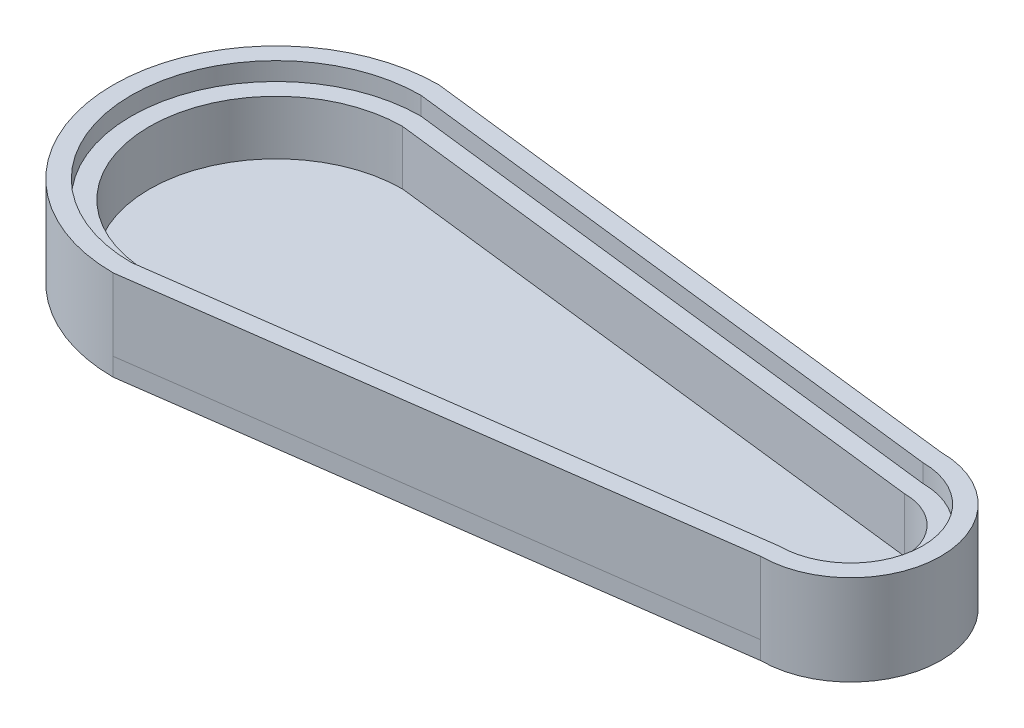
SolidWorks part; units mm, degrees
ref_plane "Front Plane" through (0, 0, 0) normal (0, 0, 1) x (1, 0, 0)
ref_plane "Top Plane" through (0, 0, 0) normal (0, 1, 0) x (1, 0, 0)
ref_plane "Right Plane" through (0, 0, 0) normal (1, 0, 0) x (0, 0, -1)
sketch "Sketch1" plane through (0, 0, 0) normal (0, 1, 0) x (1, 0, 0)
  line L0 (0, 50.8924) -> (200.0001, 27.3028)
  line L1 (199.9996, -23.3818) -> (0, -50.8924)
  line L2 (0.0003, 57.2427) -> (199.9998, 33.6531)
  line L3 (-0.0015, -57.2427) -> (199.9993, -29.7322)
  arc A0 (0, -50.8924) -> (0, 50.8924) centre (0, 0) cw
  arc A1 (199.9996, -23.3818) -> (200.0001, 27.3028) centre (199.9996, 1.9605) ccw
  arc A2 (-0.0015, -57.2427) -> (0.0003, 57.2427) centre (0, 0) cw
  arc A3 (199.9993, -29.7322) -> (199.9998, 33.6531) centre (199.9996, 1.9605) ccw
  dimension "D1" = 6.3066
extrude "Boss-Extrude1" add sketch "Sketch1" along normal blind 6.35 contours L3 A3 L2 A2
sketch "Sketch5" plane through (0, 6.35, 0) normal (0, 1, 0) x (1, 0, 0)
  line L0 (0.0003, 57.2427) -> (199.9998, 33.6531)
  line L1 (-0.0015, -57.2427) -> (199.9996, -29.7322)
  line L4 (-0.1062, 44.55) -> (199.8933, 20.9505)
  line L5 (-0.1062, -44.55) -> (199.8933, -17.0295)
  arc A0 (0.0003, 57.2427) -> (-0.0015, -57.2427) centre (0, 0) ccw
  arc A1 (0.0003, 57.2427) -> (-0.0015, -57.2427) centre (0, 0) ccw construction
  arc A2 (199.9996, -29.7322) -> (199.9998, 33.6531) centre (199.9996, 1.9605) ccw
  arc A3 (199.9993, -29.7322) -> (199.9998, 33.6531) centre (199.9996, 1.9605) ccw construction
  arc A6 (-0.1062, 44.55) -> (-0.1062, -44.55) centre (0, 0) ccw
  arc A7 (199.8933, 20.9505) -> (199.8933, -17.0295) centre (199.9996, 1.9605) cw
extrude "Boss-Extrude3" add sketch "Sketch5" along normal blind 25.4
sketch "Sketch6" plane through (0, 31.75, 0) normal (0, 1, 0) x (1, 0, 0)
  line L0 (0, 50.9) -> (199.9996, 27.3005)
  line L1 (0, -50.9) -> (199.9996, -23.3795)
  arc A0 (0, 50.9) -> (0, -50.9) centre (0, 0) ccw
  arc A1 (199.9996, -23.3795) -> (199.9996, 27.3005) centre (199.9996, 1.9605) ccw
extrude "Cut-Extrude2" cut sketch "Sketch6" against normal blind 6.35 contours A0 L1 A1 L0
sketch "Sketch3" plane through (0, 25.4, 0) normal (0, 1, 0) x (1, 0, 0)
  circle A0 centre (-47.5691, 0) radius 2.5
  arc A2 (0, 50.8924) -> (0, -50.8924) centre (0, 0) ccw construction
  circle A3 centre (221.9309, 0) radius 2.5
  arc A4 (199.9996, -23.3818) -> (200.0001, 27.3028) centre (199.9996, 1.9605) ccw construction
  point P11 (-50.8924, 0)
  point P15 (225.3418, 1.9602)
  dimension "D1" = 5
  dimension "D4" = 5
  dimension "D3" = 3.3233
  dimension "D5" = 3.4109
sketch "Sketch4" plane through (0, 25.4, 0) normal (0, 1, 0) x (1, 0, 0)
  circle A0 centre (0, 0) radius 4.5
  circle A1 centre (200.0001, 0) radius 4.5
